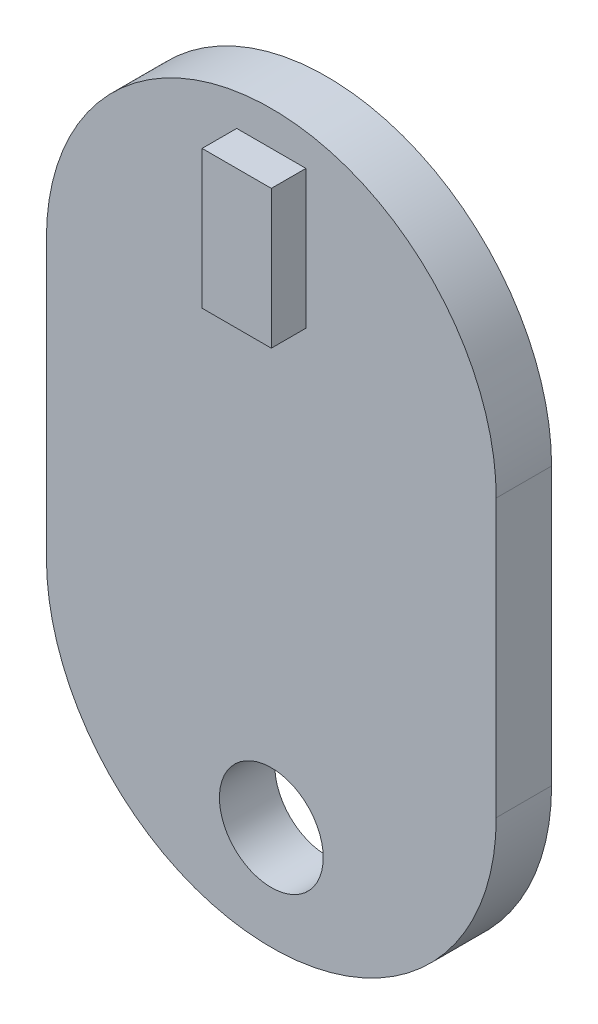
SolidWorks part; units mm, degrees
material "Fibre de verre A"
ref_plane "Plan de face" through (0, 0, 0) normal (0, 0, 1) x (1, 0, 0)
ref_plane "Plan de dessus" through (0, 0, 0) normal (0, 1, 0) x (1, 0, 0)
ref_plane "Plan de droite" through (0, 0, 0) normal (1, 0, 0) x (0, 0, -1)
sketch "Esquisse1" plane through (0, 0, 0) normal (0, 0, 1) x (1, 0, 0)
  line L0 (0, -3.5) -> (0, -11.5) construction
  line L1 (6.5, -3.5) -> (6.5, -11.5)
  line L2 (-6.5, -3.5) -> (-6.5, -11.5)
  arc A0 (6.5, -3.5) -> (-6.5, -3.5) centre (0, -3.5) ccw
  arc A1 (-6.5, -11.5) -> (6.5, -11.5) centre (0, -11.5) ccw
  circle A2 centre (0, -15) radius 1.5
  point P3 (0, -7.5)
  dimension "D2" = 21
  dimension "D4" = 3
  dimension "D1" = 13
  dimension "D3" = 3
  dimension "D5" = 3
extrude "Boss.-Extru.1" add sketch "Esquisse1" along normal blind 1.6
sketch "Esquisse2" plane through (0, 0, 1.6) normal (0, 0, 1) x (1, 0, 0)
  line L0 (-1, 2) -> (1, -2) construction
  line L1 (-1, 2) -> (1, 2)
  line L2 (-1, 2) -> (-1, -2)
  line L3 (-1, -2) -> (1, -2)
  line L4 (1, 2) -> (1, -2)
  dimension "D1" = 2
  dimension "D2" = 4
extrude "Boss.-Extru.2" add sketch "Esquisse2" along normal blind 1
sketch "Esquisse3" plane through (0, 0, 0) normal (1, 0, 0) x (0, 0, -1)
  line L0 (0, 0) -> (-21.7638, 0) construction
  line L1 (-1.6, 0) -> (-1001.6, 0)
  line L2 (-1001.6, 0) -> (-1001.6, 267.9492)
  line L3 (-1001.6, 267.9492) -> (-1.6, 0)
  line L4 (-1.6, -2) -> (-1.6, 2) construction
  dimension "D1" = 1000
  dimension "D2" = 15
revolve "Révolution1" [suppressed] add sketch "Esquisse3" angle 360 about L0
